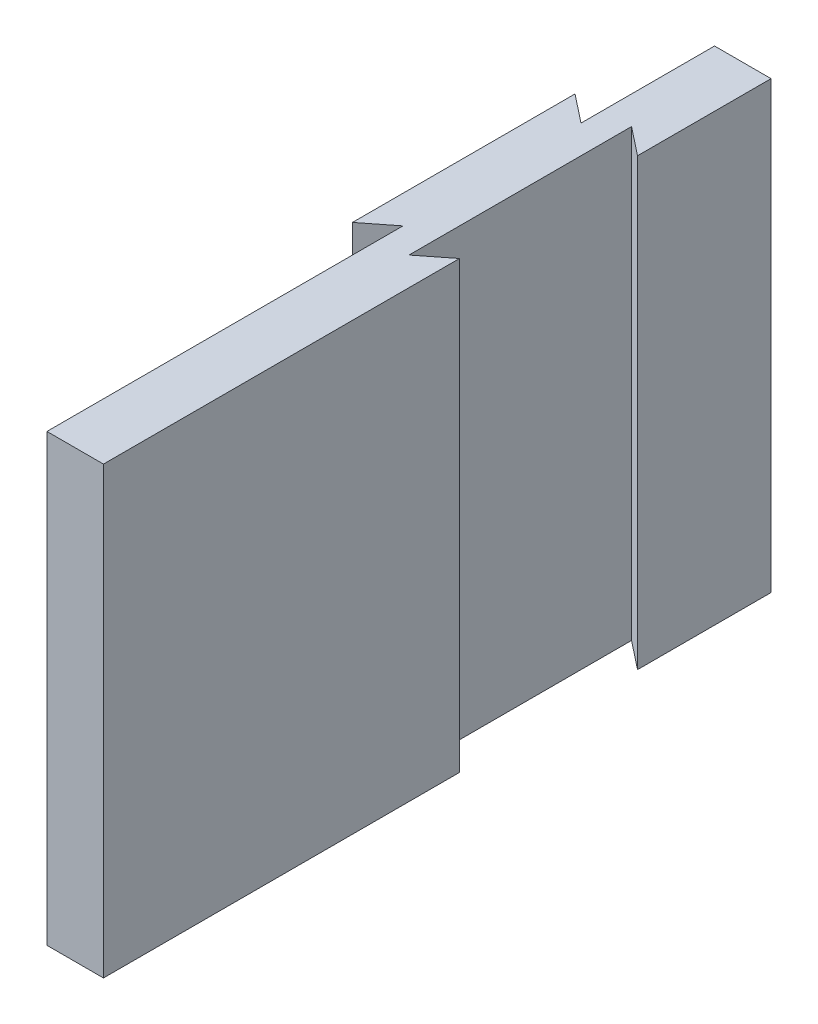
SolidWorks part; units mm, degrees
ref_plane "Front Plane" through (0, 0, 0) normal (0, 0, 1) x (1, 0, 0)
ref_plane "Top Plane" through (0, 0, 0) normal (0, 1, 0) x (1, 0, 0)
ref_plane "Right Plane" through (0, 0, 0) normal (1, 0, 0) x (0, 0, -1)
sketch "Sketch1" plane through (0, 0, 0) normal (0, 1, 0) x (1, 0, 0)
  line L0 (1.27, 4) -> (0, 5)
  line L1 (1.27, -20) -> (-1.27, -20)
  line L2 (1.27, -20) -> (1.27, 10)
  line L3 (1.27, 10) -> (-1.27, 10)
  line L4 (-1.27, -20) -> (-1.27, 10)
  line L7 (0, 5) -> (0, -5)
  line L8 (-10.1292, 0) -> (10.0424, 0) construction
  line L9 (0, 10) -> (0, -20) construction
  line L10 (1.27, 4) -> (1.27, -5)
  line L11 (1.27, -4) -> (0, -5)
  line L12 (1.27, 4) -> (1.27, -4)
  line L13 (-1.27, -4) -> (-2.54, -5)
  line L14 (-1.27, 4) -> (-2.54, 5)
  line L15 (-2.54, 5) -> (-2.54, -5)
  line L16 (-1.27, 4) -> (-1.27, -4)
  point P0 (0, 0)
  point P15 (0, 0)
  point P20 (-5.0377, 0)
  point P21 (0, 0)
  point P22 (0, 0)
  point P23 (0, 0)
  point P24 (0, 0)
  point P25 (0, 0)
  point P26 (0, 0)
  point P27 (0, 10)
  point P28 (0, -20)
  point P29 (0, 10)
  dimension "D1" = 30
  dimension "D2" = 2.54
  dimension "D3" = 8
  dimension "D4" = 10
  dimension "D5" = 1.27
  dimension "D6" = 10
extrude "Boss-Extrude1" add sketch "Sketch1" along normal blind 20 contours L2 L11 L7 L0 L3 L4 L1 | L15 L13 L16 L14
